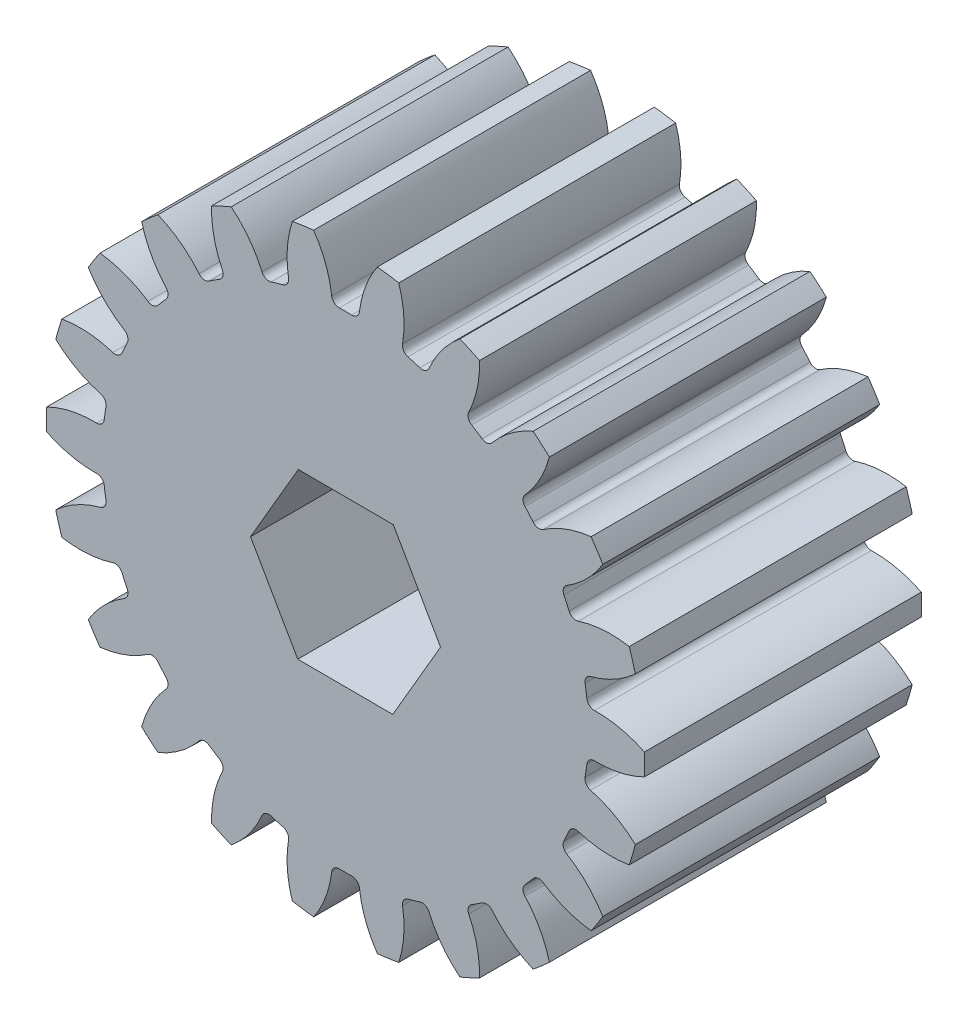
SolidWorks part; units mm, degrees
material "ABS"
ref_plane "Front Plane" through (0, 0, 0) normal (0, 0, 1) x (1, 0, 0)
ref_plane "Top Plane" through (0, 0, 0) normal (0, 1, 0) x (1, 0, 0)
ref_plane "Right Plane" through (0, 0, 0) normal (1, 0, 0) x (0, 0, -1)
sketch "Sketch1" plane through (0, 0, 0) normal (0, 0, 1) x (1, 0, 0)
  circle A0 centre (0, 0) radius 22
  circle A2 centre (0, 0) radius 24
  circle A3 centre (0, 0) radius 19.5
  dimension "D1" = 44
  dimension "D2" = 48
  dimension "D3" = 4.5
extrude "Boss-Extrude1" add sketch "Sketch1" along normal blind 19.05 and the other way blind 3.175 contours A2
sketch "Sketch3" plane through (0, 0, -3.175) normal (0, 0, -1) x (-1, 0, 0)
  line L0 (0, 0) -> (0, 24) construction
  line L1 (-1.5695, 21.9439) -> (1.5695, 21.9439) construction
  line L2 (0, 0) -> (-1.0635, 19.471) construction
  line L3 (0, 17.6319) -> (-2.6312, 24.8611) construction
  line L4 (0, 0) -> (3.4156, 23.7557) construction
  line L5 (1.5695, 21.9439) -> (4.6764, 21.4972) construction
  circle A0 centre (0, 0) radius 24 construction
  arc A1 (-3.2834, 24.7834) -> (-1.0635, 19.471) centre (-9.6529, 19.0018) cw
  arc A2 (3.2834, 24.7834) -> (1.0635, 19.471) centre (9.6529, 19.0018) ccw
  circle A3 centre (0, 0) radius 19.5 construction
  arc A4 (1.0635, 19.471) -> (-1.0635, 19.471) centre (0, 0) ccw
  arc A5 (3.2834, 24.7834) -> (-3.2834, 24.7834) centre (0, 0) ccw
  circle A6 centre (0, 0) radius 22 construction
  circle A8 centre (0, 0) radius 22 construction
  dimension "D1" = 1
  dimension "D2" = 20
  dimension "D3" = 8.182
extrude "Cut-Extrude2" cut sketch "Sketch3" against normal through all
fillet "Fillet2" radius 0.6 2 edges at (-1.0635, 19.471, 7.9375) (1.0635, 19.471, 7.9375)
pattern_circular "CirPattern2" count 22 over 360 about axis through (0, 0, 0) along (0, 0, 1) of "Cut-Extrude2", "Fillet2"
sketch "Sketch4" plane through (0, 0, 19.05) normal (0, 0, 1) x (1, 0, 0)
  line L1 (3.8362, 6.5904) -> (-3.7894, 6.6175)
  line L2 (-3.7894, 6.6175) -> (-7.6256, 0.027)
  line L3 (-7.6256, 0.027) -> (-3.8362, -6.5904)
  line L4 (-3.8362, -6.5904) -> (3.7894, -6.6175)
  line L5 (3.7894, -6.6175) -> (7.6256, -0.027)
  line L6 (7.6256, -0.027) -> (3.8362, 6.5904)
  circle A0 centre (0, 0) radius 6.604 construction
  dimension "D1" = 13.208
extrude "Cut-Extrude3" cut sketch "Sketch4" against normal through all
sketch "Diametral Pitch (for mating)" plane through (0, 0, 19.05) normal (0, 0, 1) x (1, 0, 0)
  circle A0 centre (0, 0) radius 22
  dimension "D1" = 44
equation "\"Module\"= 2mm"
equation "\"Number of Teeth\"= 22"
equation "\"D1@Sketch1\"=\"Module\"*\"Number of Teeth\""
equation "\"D2@Sketch1\"=(\"Number of Teeth\"+2) * \"Module\""
equation "\"D3@Sketch3\"=180 /\"Number of Teeth\" "
equation "\"D1@Fillet2\"=.3 * \"Module\""
equation "\"D1@CirPattern2\"=\"Number of Teeth\""
equation "\"D3@Sketch1\"=\"Module\"*if( \"Module\"=>1.25,2.25,2.4)"
equation "\"D1@Diametral Pitch (for mating)\" = \"Module\" * \"Number of Teeth\""
